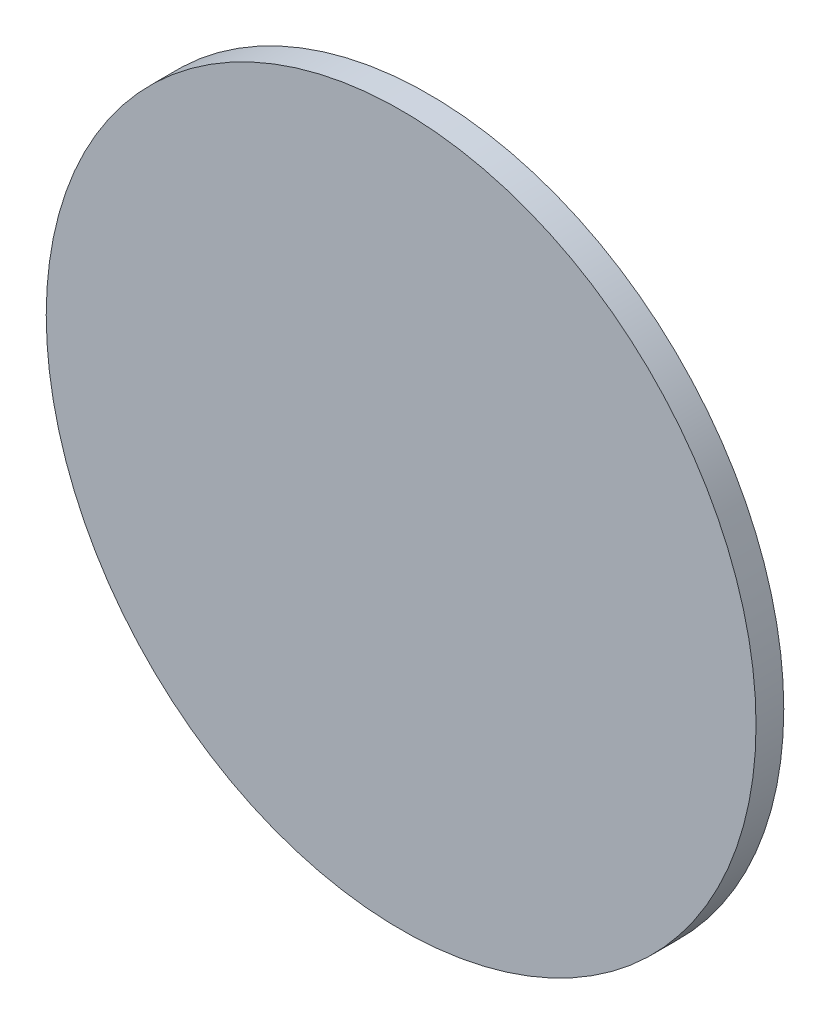
SolidWorks part; units mm, degrees
material "Bismuth"
ref_plane "Front" through (0, 0, 0) normal (0, 0, 1) x (1, 0, 0)
ref_plane "Top" through (0, 0, 0) normal (0, 1, 0) x (1, 0, 0)
ref_plane "Right" through (0, 0, 0) normal (1, 0, 0) x (0, 0, -1)
sketch "Sketch1" plane through (0, 0, 0) normal (0, 0, 1) x (1, 0, 0)
  circle A0 centre (0, 0) radius 128
extrude "Boss-Extrude1" add sketch "Sketch1" along normal blind 10
